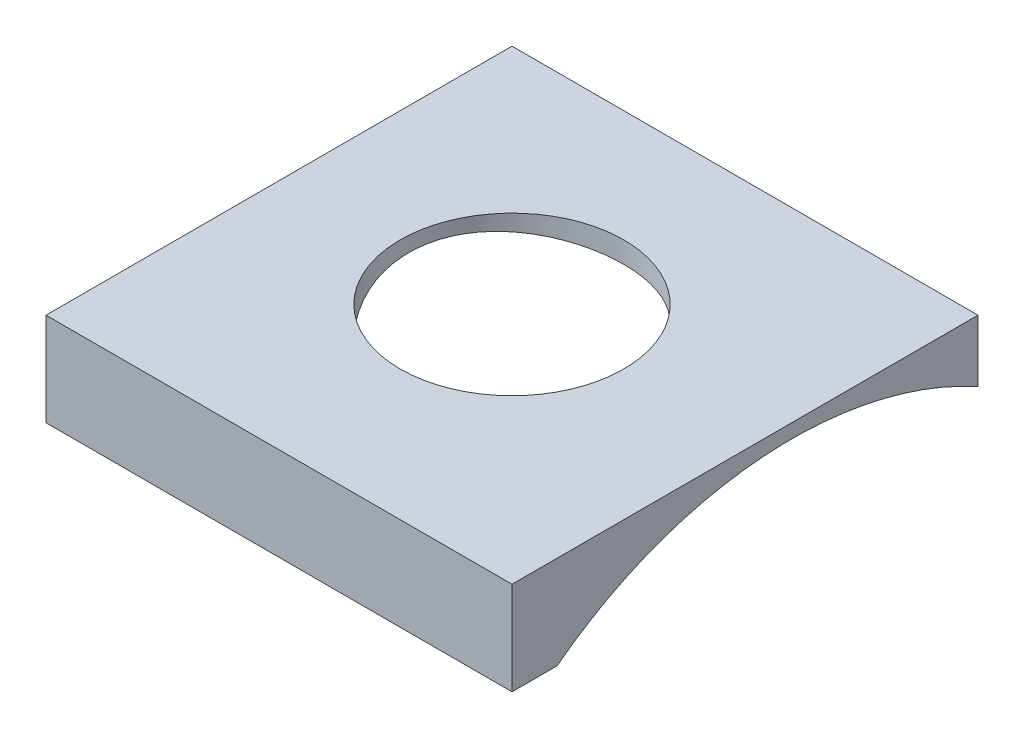
SolidWorks part; units mm, degrees
ref_plane "Front Plane" through (0, 0, 0) normal (0, 0, 1) x (1, 0, 0)
ref_plane "Top Plane" through (0, 0, 0) normal (0, 1, 0) x (1, 0, 0)
ref_plane "Right Plane" through (0, 0, 0) normal (1, 0, 0) x (0, 0, -1)
sketch "Sketch1" plane through (0, 0, 0) normal (0, 1, 0) x (1, 0, 0)
  line L1 (0, 0) -> (25, 0)
  line L2 (0, 0) -> (0, -25)
  line L3 (0, -25) -> (25, -25)
  line L4 (25, 0) -> (25, -25)
  circle A0 centre (12, -12) radius 6
  dimension "D1" = 12
  dimension "D2" = 12
  dimension "D3" = 25
  dimension "D4" = 25
  dimension "D5" = 12
extrude "Extrude1" add sketch "Sketch1" against normal blind 5
sketch "Sketch2" plane through (0, 0, 0) normal (1, 0, 0) x (0, 0, -1)
  circle A0 centre (-10, -21.5) radius 20.75
  dimension "D1" = 41.5
  dimension "D2" = 21.5
  dimension "D3" = 10
extrude "Cut-Extrude1" cut sketch "Sketch2" along normal through all
